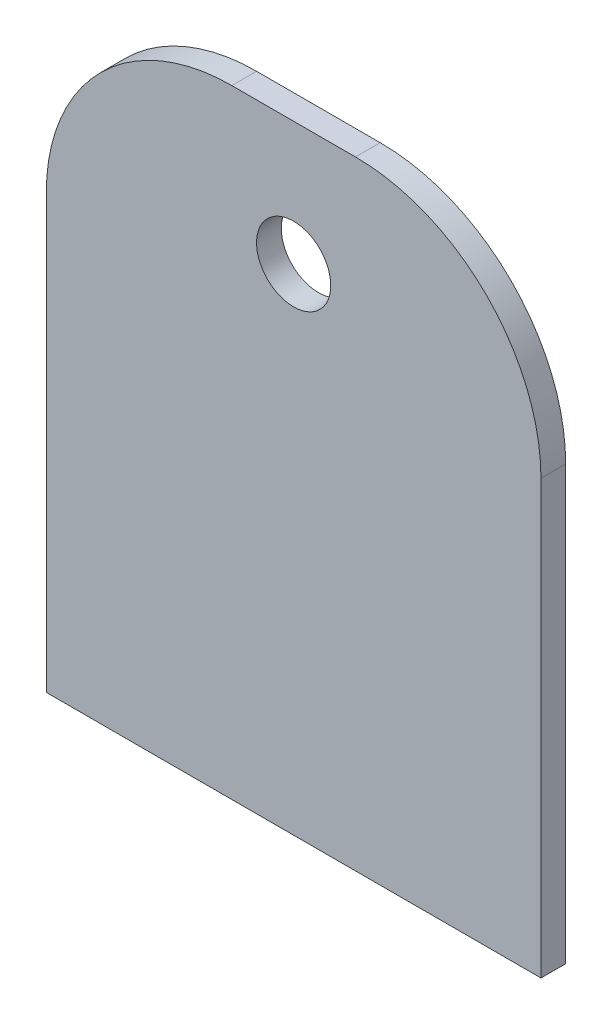
SolidWorks part; units mm, degrees
material "Stal stopowa"
ref_plane "Płaszczyzna przednia" through (0, 0, 0) normal (0, 0, 1) x (1, 0, 0)
ref_plane "Płaszczyzna górna" through (0, 0, 0) normal (0, 1, 0) x (1, 0, 0)
ref_plane "Płaszczyzna prawa" through (0, 0, 0) normal (1, 0, 0) x (0, 0, -1)
sketch "Szkic1" plane through (0, 0, 0) normal (0, 0, 1) x (1, 0, 0)
  line L1 (0, 0) -> (-40, 0)
  line L2 (0, 0) -> (0, 35)
  line L3 (-15, 50) -> (-25, 50)
  line L4 (-40, 0) -> (-40, 35)
  arc A0 (-25, 50) -> (-40, 35) centre (-25, 35) ccw
  arc A1 (0, 35) -> (-15, 50) centre (-15, 35) ccw
  circle A2 centre (-20, 40) radius 3
  point P9 (0, 50)
  dimension "D3" = 15
  dimension "D4" = 6
  dimension "D1" = 40
  dimension "D2" = 50
  dimension "D5" = 10
extrude "Dodanie-wyciągnięcie1" add sketch "Szkic1" along normal blind 2
